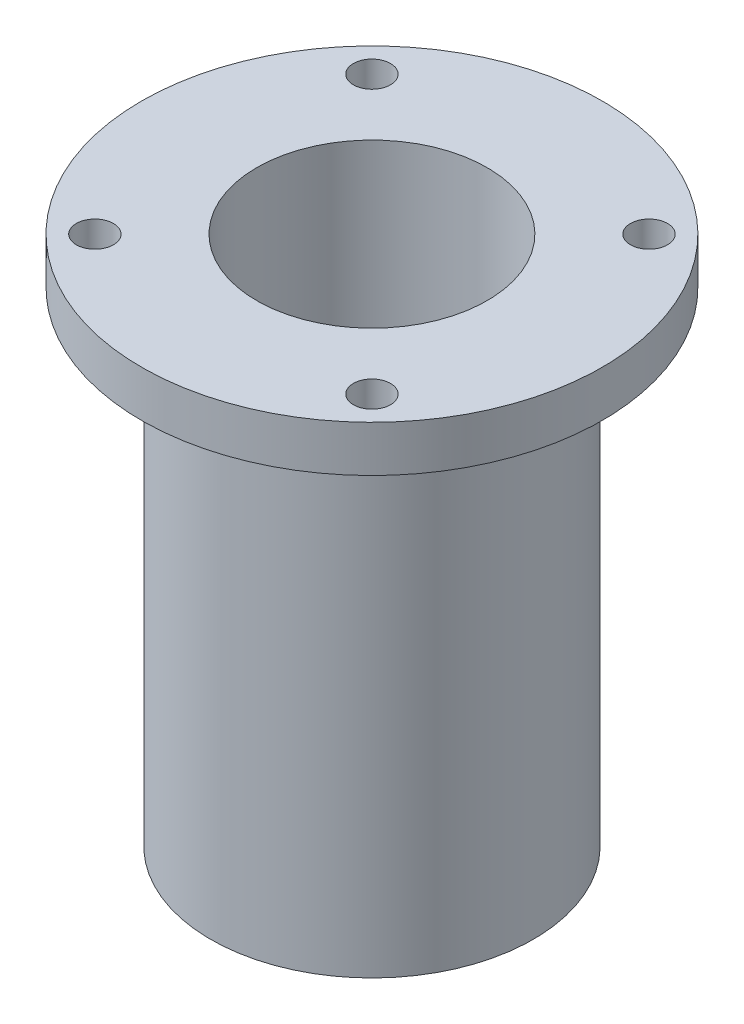
SolidWorks part; units mm, degrees
material "1023 Carbon Steel Sheet (SS)"
ref_plane "Front Plane" through (0, 0, 0) normal (0, 0, 1) x (1, 0, 0)
ref_plane "Top Plane" through (0, 0, 0) normal (0, 1, 0) x (1, 0, 0)
ref_plane "Right Plane" through (0, 0, 0) normal (1, 0, 0) x (0, 0, -1)
sketch "Sketch1" plane through (0, 0, 0) normal (0, 0, 1) x (1, 0, 0)
  line L0 (-31.75, 0) -> (-15.875, 0)
  line L1 (-15.875, 0) -> (-15.875, -63.5)
  line L2 (-15.875, -63.5) -> (0, -63.5)
  line L3 (0, -63.5) -> (0, -73.025)
  line L4 (0, -73.025) -> (-22.225, -73.025)
  line L5 (-22.225, -73.025) -> (-22.225, -6.35)
  line L6 (-22.225, -6.35) -> (-31.75, -6.35)
  line L7 (-31.75, -6.35) -> (-31.75, 0)
  line L8 (0, 0) -> (0, -73.025) construction
  point P10 (-31.75, -3.175)
  point P11 (-12.7, -57.7774)
  point P12 (0, 0)
  dimension "D1" = 63.5
  dimension "D2" = 31.75
  dimension "D3" = 9.525
  dimension "D4" = 6.35
  dimension "D5" = 31.75
  dimension "D6" = 6.35
revolve "Revolve1" add sketch "Sketch1" angle 360 about L8
hole_wizard "Pipe Tap Drill for 3/8 Tap1" positions "3DSketch1" profile "Sketch2" hole size "3/8" standard "ANSI Inch"
sketch3d "3DSketch1"
  circle A0 centre (0, -73.025, 0) radius 22.225 construction
  point P0 (0, -73.025, 0)
  point P5 (0, -50.8, 0)
sketch "Sketch2" plane through (0, -73.025, 0) normal (1, 0, 0) x (0, 0, -1)
  line L0 (0, 0) -> (0, 29.6886)
  line L1 (0, 29.6886) -> (7.1374, 25.4)
  line L2 (7.1374, 25.4) -> (7.1374, 0)
  line L5 (7.1374, 0) -> (0, 0)
  line L10 (0, 29.6886) -> (-7.1374, 25.4) construction
  line L11 (0, -6.35) -> (0, 107.95) construction
  dimension "Hole Dia." = 14.2748
  dimension "Hole Depth" = 25.4
  dimension "Drill Angle" = 118
hole_wizard "#10 Clearance Hole1" positions "3DSketch2" profile "Sketch3" hole size "#10" standard "ANSI Inch"
sketch3d "3DSketch2"
  line L0 (19.083, 0, -19.083) -> (0, 0, 0) construction
  line L2 (0, 0, 0) -> (31.75, 0, 0) construction
  line L4 (19.083, 0, -19.083) -> (22.4506, 0, -22.4506) construction
  circle A0 centre (0, 0, 0) radius 31.75 construction
  point P0 (19.083, 0, -19.083)
  point P11 (0, 31.75, 0)
  point P19 (20.3466, 0, -24.3737)
  dimension "D1" = 45
  dimension "D2" = 4.7625
sketch "Sketch3" plane through (19.083, 0, -19.083) normal (1, 0, 0) x (0, 0, 1)
  line L0 (0, 0) -> (0, 26.9338)
  line L1 (0, 26.9338) -> (2.5527, 25.4)
  line L2 (2.5527, 25.4) -> (2.5527, 0)
  line L5 (2.5527, 0) -> (0, 0)
  line L10 (0, 26.9338) -> (-2.5527, 25.4) construction
  line L11 (0, -6.35) -> (0, 107.95) construction
  dimension "Hole Dia." = 5.1054
  dimension "Hole Depth" = 25.4
  dimension "Drill Angle" = 118
pattern_circular "CirPattern1" count 4 over 360 about axis through (0, 0, 0) along (0, 1, 0) of "#10 Clearance Hole1"
